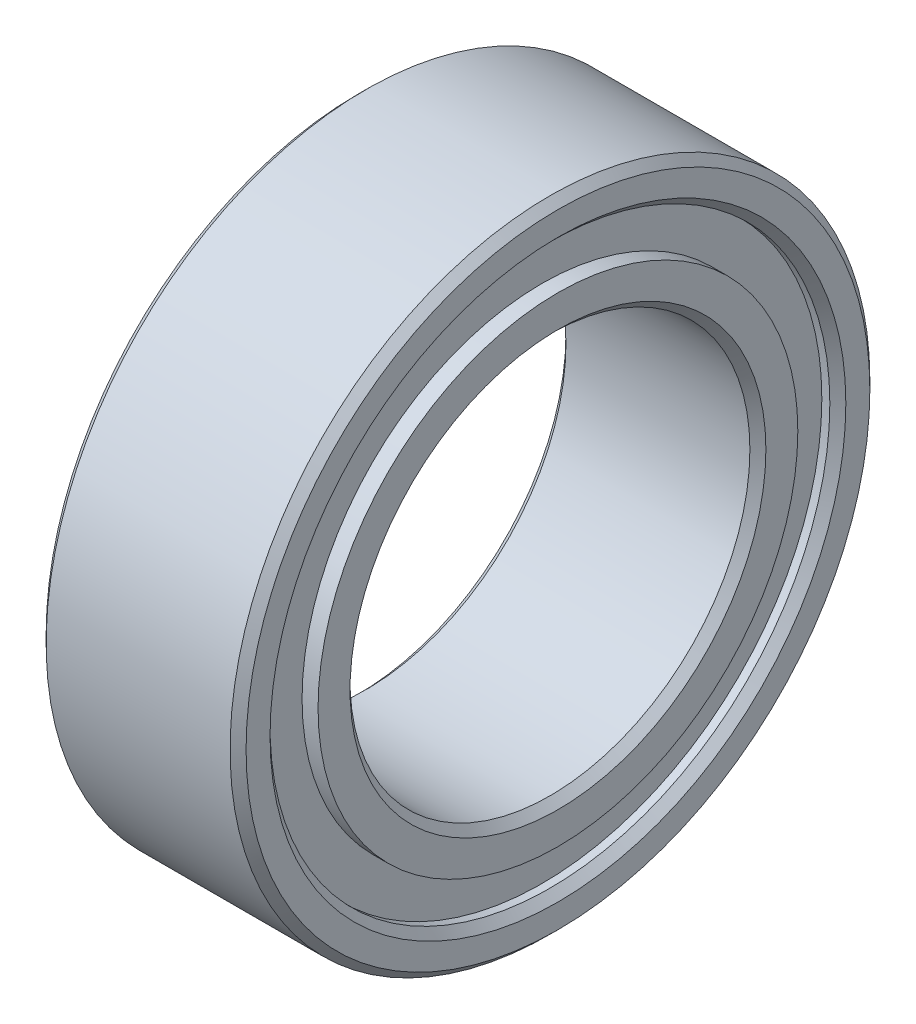
SolidWorks part; units mm, degrees
ref_plane "前视基准面" through (0, 0, 0) normal (0, 0, 1) x (1, 0, 0)
ref_plane "上视基准面" through (0, 0, 0) normal (0, 1, 0) x (1, 0, 0)
ref_plane "右视基准面" through (0, 0, 0) normal (1, 0, 0) x (0, 0, -1)
sketch "草图1" plane through (0, 0, 0) normal (1, 0, 0) x (0, 0, -1)
  circle A0 centre (0, 0) radius 2.5
  circle A1 centre (0, 0) radius 4
  dimension "D1" = 5
  dimension "D2" = 8
extrude "凸台-拉伸1" add sketch "草图1" along normal blind 2.5
sketch "草图2" plane through (2.5, 0, 0) normal (1, 0, 0) x (0, 0, -1)
  circle A0 centre (-0.0004, 0) radius 3.5
  circle A1 centre (-0.0004, 0) radius 2.9996
  circle A2 centre (0, 0) radius 4 construction
  dimension "D1" = 1
  dimension "D2" = 7
extrude "切除-拉伸1" cut sketch "草图2" against normal blind 0.2
sketch "草图3" plane through (0, 0, 0) normal (-1, 0, 0) x (0, 0, 1)
  circle A0 centre (-0.0491, 0) radius 3.5
  circle A1 centre (-0.0491, 0) radius 2.9509
  circle A2 centre (0, 0) radius 4 construction
  dimension "D1" = 7
  dimension "D2" = 1
extrude "切除-拉伸2" cut sketch "草图3" against normal blind 0.2
chamfer "倒角1" distance 0.1 angle 45 7 edges at (2.5, 0, -4) (2.5, 0, -2.5) (2.5, 0, -3.4996) (0, 0, -4) (0, 0, 2.9018) (0, 0, -2.5) (0, 0, 3.4509)
